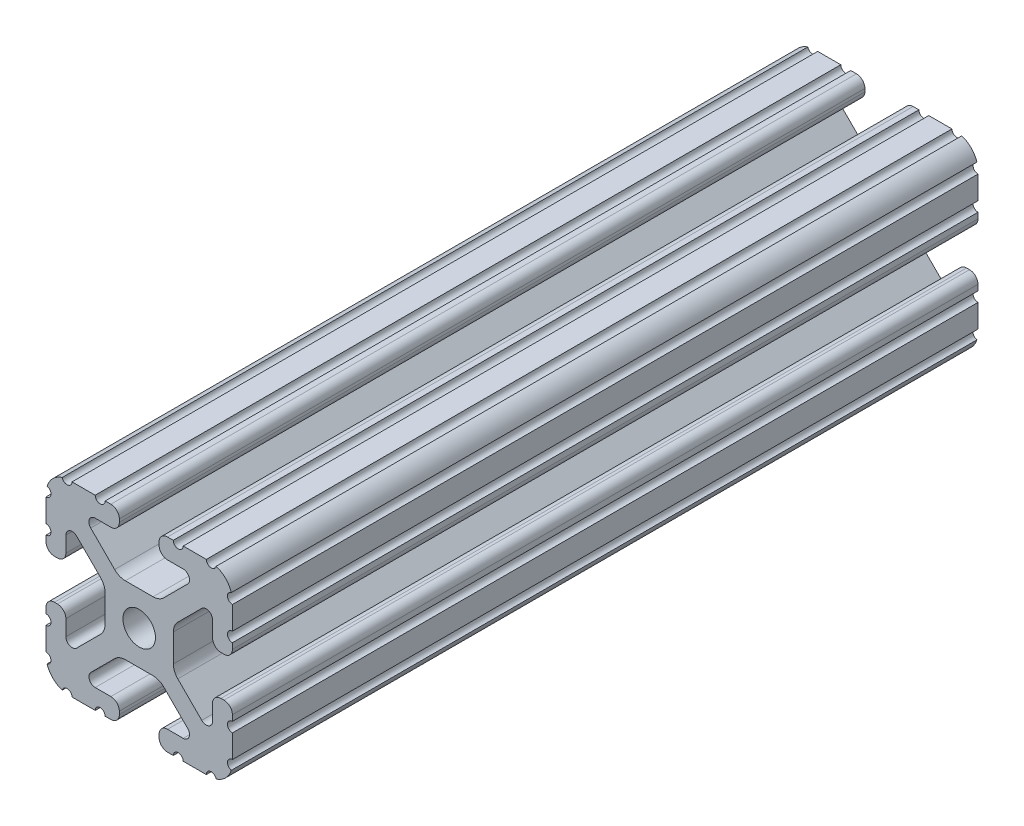
SolidWorks part; units mm, degrees
ref_plane "Front Plane" through (0, 0, 0) normal (0, 0, 1) x (1, 0, 0)
ref_plane "Top Plane" through (0, 0, 0) normal (0, 1, 0) x (1, 0, 0)
ref_plane "Right Plane" through (0, 0, 0) normal (1, 0, 0) x (0, 0, -1)
sketch "Sketch2" plane through (0, 0, 0) normal (0, 0, 1) x (1, 0, 0)
  line L0 (0, 19.05) -> (0, -19.05) construction
  line L1 (-19.05, 0) -> (19.05, 0) construction
  line L2 (4.064, -19.05) -> (19.05, -19.05)
  line L3 (19.05, -19.05) -> (19.05, -4.064)
  line L4 (4.064, -19.05) -> (4.064, -14.986)
  line L5 (4.064, -14.986) -> (12.1123, -14.986)
  line L6 (12.1123, -14.986) -> (4.1113, -6.985)
  line L7 (0, 0) -> (19.05, -19.05) construction
  line L8 (19.05, -4.064) -> (14.986, -4.064)
  line L9 (14.986, -4.064) -> (14.986, -12.1123)
  line L10 (14.986, -12.1123) -> (6.985, -4.1113)
  circle A0 centre (0, 0) radius 3.3274
  arc A1 (8.9963, -14.986) -> (9.909, -12.7826) centre (8.9963, -13.6953) ccw construction
  point P8 (0, -6.985)
  dimension "Center Hole Diameter" = 6.6548
  dimension "Rail Height" = 38.1
  dimension "Rail Width" = 38.1
  dimension "T-Slot Width" = 8.128
  dimension "Slot Inner Width" = 20.574
  dimension "Thickness" = 4.064
  dimension "Slot Depth" = 8.001
  dimension "D1" = 4.064
sketch "Sketch3" plane through (0, 0, 0) normal (1, 0, 0) x (0, 0, -1)
  line L0 (-76.2, -19.05) -> (76.2, -19.05) construction
  line L1 (-68.58, 0) -> (68.58, 0) construction
  dimension "Length" = 152.4
  dimension "D1" = 137.16
sketch "Sketch4" plane through (0, 0, 0) normal (0, 0, 1) x (1, 0, 0)
  line L0 (5.7912, -19.05) -> (14.3002, -19.05)
  line L1 (4.064, -19.05) -> (19.05, -19.05) construction
  line L2 (4.064, -19.05) -> (4.064, -14.986) construction
  line L3 (4.064, -14.986) -> (12.1123, -14.986) construction
  line L4 (4.064, -16.7132) -> (4.064, -17.3228)
  line L5 (5.7912, -14.986) -> (8.9963, -14.986)
  line L6 (0, -6.985) -> (2.833, -6.985)
  line L7 (12.1123, -14.986) -> (4.1113, -6.985) construction
  line L8 (5.0152, -7.8889) -> (9.909, -12.7826)
  line L9 (19.05, -19.05) -> (19.05, -4.064) construction
  line L10 (14.986, -12.1123) -> (6.985, -4.1113) construction
  line L11 (14.986, -4.064) -> (14.986, -12.1123) construction
  line L12 (14.986, -8.9963) -> (14.986, -5.7912)
  line L13 (19.05, -4.064) -> (14.986, -4.064) construction
  line L14 (16.7132, -4.064) -> (17.3228, -4.064)
  line L15 (19.05, -5.7912) -> (19.05, -14.3002)
  line L16 (12.7826, -9.909) -> (7.8889, -5.0152)
  line L17 (6.985, 0) -> (6.985, -2.833)
  line L18 (-19.05, 0) -> (19.05, 0) construction
  line L19 (0, -6.985) -> (0, -3.3274)
  line L20 (0, 19.05) -> (0, -19.05) construction
  line L21 (6.985, 0) -> (3.3274, 0)
  arc A0 (4.064, -17.3228) -> (5.7912, -19.05) centre (5.7912, -17.3228) ccw
  arc A2 (4.064, -16.7132) -> (5.7912, -14.986) centre (5.7912, -16.7132) cw
  arc A3 (8.9963, -14.986) -> (9.909, -12.7826) centre (8.9963, -13.6953) ccw
  arc A4 (2.833, -6.985) -> (5.0152, -7.8889) centre (2.833, -10.0711) cw
  arc A5 (14.3002, -19.05) -> (19.05, -14.3002) centre (14.3002, -14.3002) ccw
  arc A6 (12.7826, -9.909) -> (14.986, -8.9963) centre (13.6953, -8.9963) ccw
  arc A7 (14.986, -5.7912) -> (16.7132, -4.064) centre (16.7132, -5.7912) cw
  arc A8 (17.3228, -4.064) -> (19.05, -5.7912) centre (17.3228, -5.7912) cw
  arc A9 (7.8889, -5.0152) -> (6.985, -2.833) centre (10.0711, -2.833) cw
  circle A10 centre (0, 0) radius 3.3274 construction
  arc A11 (0, -3.3274) -> (3.3274, 0) centre (0, 0) ccw
  dimension "D1" = 4.7498
  dimension "D2" = 3.0861
  dimension "D3" = 1.7272
extrude "Boss-Extrude1" add sketch "Sketch4" along normal mid plane 152.4
sketch "Sketch5" plane through (0, 0, 0) normal (0, 0, 1) x (1, 0, 0)
  line L0 (4.064, -19.05) -> (19.05, -19.05) construction
  line L1 (5.7912, -14.986) -> (8.9963, -14.986) construction
  line L3 (0, 0) -> (19.05, -19.05) construction
  line L4 (8.9963, -14.986) -> (8.9963, -19.05) construction
  line L5 (12.1123, -14.986) -> (4.1113, -6.985) construction
  circle A0 centre (14.7395, -19.05) radius 1.016
  circle A1 centre (7.9803, -19.05) radius 1.016
  circle A2 centre (19.05, -14.7395) radius 1.016
  circle A3 centre (19.05, -7.9803) radius 1.016
  point P10 (7.3938, -14.986)
  point P12 (13.6953, -8.9963)
  dimension "D1" = 2.032
extrude "Cut-Extrude1" cut sketch "Sketch5" against normal through all both and the other way through all
mirror "Mirror1" about plane through (0, 0, 0) normal (1, 0, 0) of bodies 137 134
mirror "Mirror2" about plane through (0, 0, 0) normal (0, 1, 0) of bodies 135
equation "\"D1@Boss-Extrude1\"=\"Length@Sketch3\""
equation "\"D1@Sketch2\"=\"Thickness@Sketch2\""
equation "\"D2@Sketch4\"=\"Slot Inner Width@Sketch2\"*0.15"
equation "\"D1@Sketch4\"=\"D3@Sketch4\"*2.75"
equation "\"D3@Sketch4\"=\"Thickness@Sketch2\"*0.425"
equation "\"D1@Sketch5\"=\"Thickness@Sketch2\"*0.5"
equation "\"D1@Sketch3\"=\"Length@Sketch3\"*0.9"
